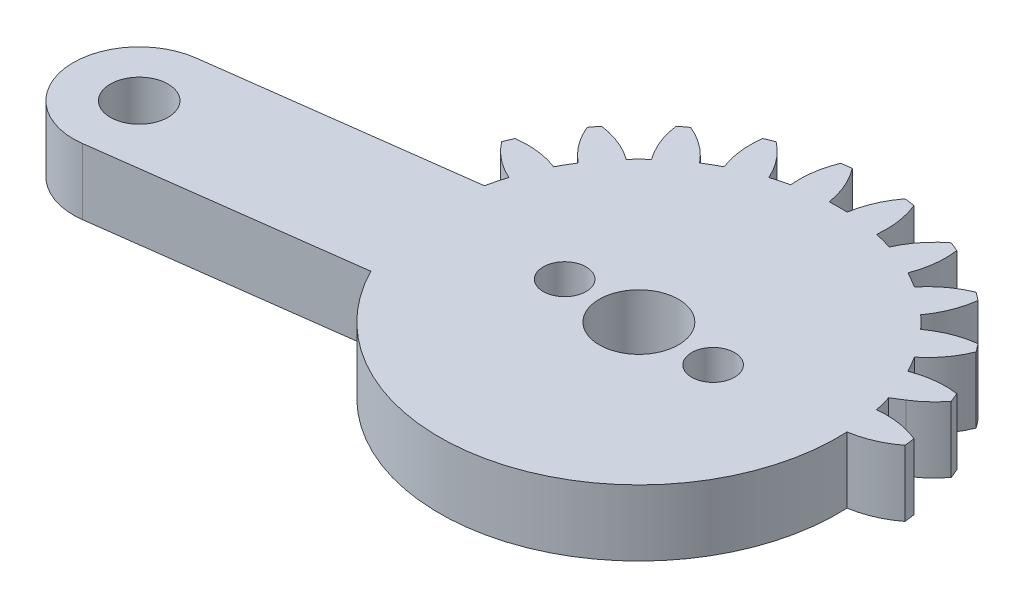
SolidWorks part; units mm, degrees
ref_plane "Front Plane" through (0, 0, 0) normal (0, 0, 1) x (1, 0, 0)
ref_plane "Top Plane" through (0, 0, 0) normal (0, 1, 0) x (1, 0, 0)
ref_plane "Right Plane" through (0, 0, 0) normal (1, 0, 0) x (0, 0, -1)
sketch "Sketch1" plane through (0, 0, 0) normal (0, 1, 0) x (1, 0, 0)
  line L0 (20.6437, 4) -> (2.0816, 4)
  line L1 (2.0816, -4) -> (20.6437, -4)
  arc A0 (2.0816, 4) -> (3.5217, 5.3071) centre (-0.7683, 8.5867) ccw
  arc A1 (3.5217, 5.3071) -> (3.2829, 5.8838) centre (-10.1063, 0) ccw
  arc A2 (3.2829, 5.8838) -> (0.6271, 5.5703) centre (2.5684, 0.5313) ccw
  arc A3 (0.6271, 5.5703) -> (0.0844, 6.5103) centre (-10.1063, 0) ccw
  arc A4 (0.0844, 6.5103) -> (1.6838, 8.6535) centre (-3.3089, 10.711) ccw
  arc A5 (1.6838, 8.6535) -> (1.3038, 9.1487) centre (-10.1063, 0) ccw
  arc A6 (1.3038, 9.1487) -> (-1.1803, 8.1585) centre (1.999, 3.7936) ccw
  arc A7 (-1.1803, 8.1585) -> (-1.9479, 8.926) centre (-10.1063, 0) ccw
  arc A8 (-1.9479, 8.926) -> (-0.9576, 11.4102) centre (-6.3127, 12.1053) ccw
  arc A9 (-0.9576, 11.4102) -> (-1.4528, 11.7901) centre (-10.1063, 0) ccw
  arc A10 (-1.4528, 11.7901) -> (-3.596, 10.1907) centre (0.6046, 6.7975) ccw
  arc A11 (-3.596, 10.1907) -> (-4.5361, 10.7334) centre (-10.1063, 0) ccw
  arc A12 (-4.5361, 10.7334) -> (-4.2225, 13.3892) centre (-9.5751, 12.6747) ccw
  arc A13 (-4.2225, 13.3892) -> (-4.7992, 13.6281) centre (-10.1063, 0) ccw
  arc A14 (-4.7992, 13.6281) -> (-6.4554, 11.5285) centre (-1.5196, 9.3381) ccw
  arc A15 (-6.4554, 11.5285) -> (-7.5039, 11.8094) centre (-10.1063, 0) ccw
  arc A16 (-7.5039, 11.8094) -> (-7.8884, 14.4558) centre (-12.8736, 12.3803) ccw
  arc A17 (-7.8884, 14.4558) -> (-8.5072, 14.5373) centre (-10.1063, 0) ccw
  arc A18 (-8.5072, 14.5373) -> (-9.5636, 12.0806) centre (-4.2291, 11.2423) ccw
  arc A19 (-9.5636, 12.0806) -> (-10.6491, 12.0806) centre (-10.1063, 0) ccw
  arc A20 (-10.6491, 12.0806) -> (-11.7054, 14.5373) centre (-15.9836, 11.2423) ccw
  arc A21 (-11.7054, 14.5373) -> (-12.3243, 14.4558) centre (-10.1063, 0) ccw
  arc A22 (-12.3243, 14.4558) -> (-12.7088, 11.8094) centre (-7.3391, 12.3803) ccw
  arc A23 (-12.7088, 11.8094) -> (-13.7573, 11.5285) centre (-10.1063, 0) ccw
  arc A24 (-13.7573, 11.5285) -> (-15.4135, 13.6281) centre (-18.6931, 9.3381) ccw
  arc A25 (-15.4135, 13.6281) -> (-15.9901, 13.3892) centre (-10.1063, 0) ccw
  arc A26 (-15.9901, 13.3892) -> (-15.6766, 10.7334) centre (-10.6376, 12.6747) ccw
  arc A27 (-15.6766, 10.7334) -> (-16.6166, 10.1907) centre (-10.1063, 0) ccw
  arc A28 (-16.6166, 10.1907) -> (-18.7599, 11.7901) centre (-20.8173, 6.7975) ccw
  arc A29 (-18.7599, 11.7901) -> (-19.255, 11.4102) centre (-10.1063, 0) ccw
  arc A30 (-19.255, 11.4102) -> (-18.2648, 8.926) centre (-13.9, 12.1053) ccw
  arc A31 (-18.2648, 8.926) -> (-19.0324, 8.1585) centre (-10.1063, 0) ccw
  arc A32 (-19.0324, 8.1585) -> (-21.5165, 9.1487) centre (-22.2117, 3.7936) ccw
  arc A33 (-21.5165, 9.1487) -> (-21.8965, 8.6535) centre (-10.1063, 0) ccw
  arc A34 (-21.8965, 8.6535) -> (-20.2971, 6.5103) centre (-16.9038, 10.711) ccw
  arc A35 (-20.2971, 6.5103) -> (-20.8398, 5.5703) centre (-10.1063, 0) ccw
  arc A36 (-20.8398, 5.5703) -> (-23.4956, 5.8838) centre (-22.7811, 0.5313) ccw
  arc A37 (-23.4956, 5.8838) -> (-23.7344, 5.3071) centre (-10.1063, 0) ccw
  arc A38 (-23.7344, 5.3071) -> (-21.6348, 3.6509) centre (-19.4444, 8.5867) ccw
  arc A39 (-21.6348, 3.6509) -> (-21.9157, 2.6025) centre (-10.1063, 0) ccw
  arc A40 (-21.9157, 2.6025) -> (-24.5622, 2.2179) centre (-22.4867, -2.7673) ccw
  arc A41 (-24.5622, 2.2179) -> (-24.6437, 1.5991) centre (-10.1063, 0) ccw
  arc A42 (-24.6437, 1.5991) -> (-22.1869, 0.5427) centre (-21.3486, 5.8773) ccw
  arc A43 (-22.1869, 0.5427) -> (-22.1869, -0.5427) centre (-10.1063, 0) ccw
  arc A44 (-22.1869, -0.5427) -> (-24.6437, -1.5991) centre (-21.3486, -5.8773) ccw
  arc A45 (-24.6437, -1.5991) -> (-24.5622, -2.2179) centre (-10.1063, 0) ccw
  arc A46 (-24.5622, -2.2179) -> (-21.9157, -2.6025) centre (-22.4867, 2.7673) ccw
  arc A47 (-21.9157, -2.6025) -> (-21.6348, -3.6509) centre (-10.1063, 0) ccw
  arc A48 (-21.6348, -3.6509) -> (-23.7344, -5.3071) centre (-19.4444, -8.5867) ccw
  arc A49 (-23.7344, -5.3071) -> (-23.4956, -5.8838) centre (-10.1063, 0) ccw
  arc A50 (-23.4956, -5.8838) -> (-20.8398, -5.5703) centre (-22.7811, -0.5313) ccw
  arc A51 (-20.8398, -5.5703) -> (-20.2971, -6.5103) centre (-10.1063, 0) ccw
  arc A52 (-20.2971, -6.5103) -> (-21.8965, -8.6535) centre (-16.9038, -10.711) ccw
  arc A53 (-21.8965, -8.6535) -> (-21.5165, -9.1487) centre (-10.1063, 0) ccw
  arc A54 (-21.5165, -9.1487) -> (-19.0324, -8.1585) centre (-22.2117, -3.7936) ccw
  arc A55 (-19.0324, -8.1585) -> (-18.2648, -8.926) centre (-10.1063, 0) ccw
  arc A56 (-18.2648, -8.926) -> (-19.255, -11.4102) centre (-13.9, -12.1053) ccw
  arc A57 (-19.255, -11.4102) -> (-18.7599, -11.7901) centre (-10.1063, 0) ccw
  arc A58 (-18.7599, -11.7901) -> (-16.6166, -10.1907) centre (-20.8173, -6.7975) ccw
  arc A59 (-16.6166, -10.1907) -> (-15.6766, -10.7334) centre (-10.1063, 0) ccw
  arc A60 (-15.6766, -10.7334) -> (-15.9901, -13.3892) centre (-10.6376, -12.6747) ccw
  arc A61 (-15.9901, -13.3892) -> (-15.4135, -13.6281) centre (-10.1063, 0) ccw
  arc A62 (-15.4135, -13.6281) -> (-13.7573, -11.5285) centre (-18.6931, -9.3381) ccw
  arc A63 (-13.7573, -11.5285) -> (-12.7088, -11.8094) centre (-10.1063, 0) ccw
  arc A64 (-12.7088, -11.8094) -> (-12.3243, -14.4558) centre (-7.3391, -12.3803) ccw
  arc A65 (-12.3243, -14.4558) -> (-11.7054, -14.5373) centre (-10.1063, 0) ccw
  arc A66 (-11.7054, -14.5373) -> (-10.6491, -12.0806) centre (-15.9836, -11.2423) ccw
  arc A67 (-10.6491, -12.0806) -> (-9.5636, -12.0806) centre (-10.1063, 0) ccw
  arc A68 (-9.5636, -12.0806) -> (-8.5072, -14.5373) centre (-4.2291, -11.2423) ccw
  arc A69 (-8.5072, -14.5373) -> (-7.8884, -14.4558) centre (-10.1063, 0) ccw
  arc A70 (-7.8884, -14.4558) -> (-7.5039, -11.8094) centre (-12.8736, -12.3803) ccw
  arc A71 (-7.5039, -11.8094) -> (-6.4554, -11.5285) centre (-10.1063, 0) ccw
  arc A72 (-6.4554, -11.5285) -> (-4.7992, -13.6281) centre (-1.5196, -9.3381) ccw
  arc A73 (-4.7992, -13.6281) -> (-4.2225, -13.3892) centre (-10.1063, 0) ccw
  arc A74 (-4.2225, -13.3892) -> (-4.5361, -10.7334) centre (-9.5751, -12.6747) ccw
  arc A75 (-4.5361, -10.7334) -> (-3.596, -10.1907) centre (-10.1063, 0) ccw
  arc A76 (-3.596, -10.1907) -> (-1.4528, -11.7901) centre (0.6046, -6.7975) ccw
  arc A77 (-1.4528, -11.7901) -> (-0.9576, -11.4102) centre (-10.1063, 0) ccw
  arc A78 (-0.9576, -11.4102) -> (-1.9479, -8.926) centre (-6.3127, -12.1053) ccw
  arc A79 (-1.9479, -8.926) -> (-1.1803, -8.1585) centre (-10.1063, 0) ccw
  arc A80 (-1.1803, -8.1585) -> (1.3038, -9.1487) centre (1.999, -3.7936) ccw
  arc A81 (1.3038, -9.1487) -> (1.6838, -8.6535) centre (-10.1063, 0) ccw
  arc A82 (1.6838, -8.6535) -> (0.0844, -6.5103) centre (-3.3089, -10.711) ccw
  arc A83 (0.0844, -6.5103) -> (0.6271, -5.5703) centre (-10.1063, 0) ccw
  arc A84 (0.6271, -5.5703) -> (3.2829, -5.8838) centre (2.5684, -0.5313) ccw
  arc A85 (3.2829, -5.8838) -> (3.5217, -5.3071) centre (-10.1063, 0) ccw
  arc A86 (3.5217, -5.3071) -> (2.0816, -4) centre (-0.7683, -8.5867) ccw
  arc A87 (20.6437, -4) -> (20.6437, 4) centre (20.6437, 0) ccw
  circle A88 centre (-10.1063, 0) radius 1.5
  circle A89 centre (20.6437, 0) radius 1.5
  dimension "D1" = 3
  dimension "D2" = 3
extrude "Boss-Extrude1" add sketch "Sketch1" along normal blind 4
sketch "Sketch3" plane through (0, 4, 0) normal (0, 1, 0) x (1, 0, 0)
  line L0 (-10.1063, 0) -> (-40.8563, 0) construction
  line L1 (-10.1063, 0) -> (-36.8754, -3.5242)
  line L2 (-10.6284, 3.9658) -> (-37.3975, 0.4416)
  line L3 (-9.5842, -3.9658) -> (-36.3532, -7.49)
  line L4 (-10.1063, 0) -> (-4.5096, 13.5117) construction
  line L5 (-10.1063, 0) -> (-8.1974, 14.4999) construction
  circle A0 centre (-10.1063, 0) radius 1.5
  circle A1 centre (20.6437, 0) radius 1.5 construction
  circle A2 centre (20.6437, 0) radius 1.5
  circle A3 centre (-36.8754, -3.5242) radius 1.75
  circle A4 centre (-36.8754, -3.5242) radius 4
  circle A5 centre (-10.1063, 0) radius 4
  arc A6 (-4.2225, 13.3892) -> (-4.7992, 13.6281) centre (-10.1063, 0) ccw construction
  arc A7 (-7.8884, 14.4558) -> (-8.5072, 14.5373) centre (-10.1063, 0) ccw construction
  dimension "D2" = 3
  dimension "D5" = 3.5
  dimension "D6" = 8
  dimension "D7" = 8
  dimension "D1" = 27
  dimension "D4" = 7.5
extrude "Boss-Extrude2" add sketch "Sketch3" against normal blind 4
sketch "Sketch4" plane through (0, 4, 0) normal (0, 1, 0) x (1, 0, 0)
  line L0 (20.6437, 4) -> (2.0816, 4) construction
  line L1 (2.0816, -4) -> (20.6437, -4) construction
  line L2 (20.6437, 4) -> (2.0816, 4)
  line L3 (2.0816, -4) -> (20.6437, -4)
  line L4 (2.0816, 4) -> (1.4381, 3.6001)
  line L5 (-21.6245, -5.5509) -> (-20.8986, -5.4553)
  line L6 (-10.1063, 0) -> (0.0844, 6.5103) construction
  line L7 (-10.1063, 0) -> (1.9742, 0.5427) construction
  line L8 (-24.5755, 2.1296) -> (-37.3975, 0.4416)
  line L9 (-36.3532, -7.49) -> (-23.5312, -5.8019)
  line L10 (2.0816, -4) -> (20.6437, -4)
  line L11 (20.6437, 4) -> (2.0816, 4)
  line L12 (-21.9429, 2.4762) -> (-37.3975, 0.4416)
  line L13 (-36.3532, -7.49) -> (-21.6245, -5.5509)
  line L14 (2.0816, -4) -> (20.6437, -4)
  line L15 (20.6437, 4) -> (2.0816, 4)
  circle A0 centre (-10.1063, 0) radius 12.0927
  arc A1 (3.2829, 5.8838) -> (0.6271, 5.5703) centre (2.5684, 0.5313) ccw construction
  arc A2 (3.5217, 5.3071) -> (3.2829, 5.8838) centre (-10.1063, 0) ccw construction
  arc A3 (2.0816, 4) -> (3.5217, 5.3071) centre (-0.7683, 8.5867) ccw construction
  arc A4 (20.6437, -4) -> (20.6437, 4) centre (20.6437, 0) ccw construction
  arc A5 (3.5217, -5.3071) -> (2.0816, -4) centre (-0.7683, -8.5867) ccw construction
  arc A6 (3.2829, -5.8838) -> (3.5217, -5.3071) centre (-10.1063, 0) ccw construction
  arc A7 (0.6271, -5.5703) -> (3.2829, -5.8838) centre (2.5684, -0.5313) ccw construction
  arc A8 (3.2829, 5.8838) -> (0.6271, 5.5703) centre (2.5684, 0.5313) ccw
  arc A9 (3.5217, 5.3071) -> (3.2829, 5.8838) centre (-10.1063, 0) ccw
  arc A10 (2.0816, 4) -> (3.5217, 5.3071) centre (-0.7683, 8.5867) ccw
  arc A11 (20.6437, -4) -> (20.6437, 4) centre (20.6437, 0) ccw
  arc A12 (3.5217, -5.3071) -> (2.0816, -4) centre (-0.7683, -8.5867) ccw
  arc A13 (3.2829, -5.8838) -> (3.5217, -5.3071) centre (-10.1063, 0) ccw
  arc A14 (0.6271, -5.5703) -> (3.2829, -5.8838) centre (2.5684, -0.5313) ccw
  arc A15 (1.9742, 0.5427) -> (4.431, 1.5991) centre (1.1359, 5.8773) ccw
  arc A16 (4.3495, 2.2179) -> (1.7031, 2.6025) centre (2.274, -2.7673) ccw
  arc A17 (4.431, 1.5991) -> (4.3495, 2.2179) centre (-10.1063, 0) ccw
  arc A95 (-21.6348, 3.6509) -> (-21.9157, 2.6025) centre (-10.1063, 0) ccw
  arc A96 (-37.3975, 0.4416) -> (-36.3532, -7.49) centre (-36.8754, -3.5242) ccw
  arc A97 (-20.2971, -6.5103) -> (-21.8965, -8.6535) centre (-16.9038, -10.711) ccw
  arc A98 (-21.8965, -8.6535) -> (-21.5165, -9.1487) centre (-10.1063, 0) ccw
  arc A99 (-21.5165, -9.1487) -> (-19.0324, -8.1585) centre (-22.2117, -3.7936) ccw
  arc A100 (-19.0324, -8.1585) -> (-18.2648, -8.926) centre (-10.1063, 0) ccw
  arc A101 (-18.2648, -8.926) -> (-19.255, -11.4102) centre (-13.9, -12.1053) ccw
  arc A102 (-19.255, -11.4102) -> (-18.7599, -11.7901) centre (-10.1063, 0) ccw
  arc A103 (-18.7599, -11.7901) -> (-16.6166, -10.1907) centre (-20.8173, -6.7975) ccw
  arc A104 (-16.6166, -10.1907) -> (-15.6766, -10.7334) centre (-10.1063, 0) ccw
  arc A105 (-15.6766, -10.7334) -> (-15.9901, -13.3892) centre (-10.6376, -12.6747) ccw
  arc A106 (-15.9901, -13.3892) -> (-15.4135, -13.6281) centre (-10.1063, 0) ccw
  arc A107 (-15.4135, -13.6281) -> (-13.7573, -11.5285) centre (-18.6931, -9.3381) ccw
  arc A108 (-13.7573, -11.5285) -> (-12.7088, -11.8094) centre (-10.1063, 0) ccw
  arc A109 (-12.7088, -11.8094) -> (-12.3243, -14.4558) centre (-7.3391, -12.3803) ccw
  arc A110 (-12.3243, -14.4558) -> (-11.7054, -14.5373) centre (-10.1063, 0) ccw
  arc A111 (-11.7054, -14.5373) -> (-10.6491, -12.0806) centre (-15.9836, -11.2423) ccw
  arc A112 (-10.6491, -12.0806) -> (-9.5636, -12.0806) centre (-10.1063, 0) ccw
  arc A113 (-9.5636, -12.0806) -> (-8.5072, -14.5373) centre (-4.2291, -11.2423) ccw
  arc A114 (-8.5072, -14.5373) -> (-7.8884, -14.4558) centre (-10.1063, 0) ccw
  arc A115 (-7.8884, -14.4558) -> (-7.5039, -11.8094) centre (-12.8736, -12.3803) ccw
  arc A116 (-7.5039, -11.8094) -> (-6.4554, -11.5285) centre (-10.1063, 0) ccw
  arc A117 (-6.4554, -11.5285) -> (-4.7992, -13.6281) centre (-1.5196, -9.3381) ccw
  arc A118 (-4.7992, -13.6281) -> (-4.2225, -13.3892) centre (-10.1063, 0) ccw
  arc A119 (-4.2225, -13.3892) -> (-4.5361, -10.7334) centre (-9.5751, -12.6747) ccw
  arc A120 (-4.5361, -10.7334) -> (-3.596, -10.1907) centre (-10.1063, 0) ccw
  arc A121 (-3.596, -10.1907) -> (-1.4528, -11.7901) centre (0.6046, -6.7975) ccw
  arc A122 (-1.4528, -11.7901) -> (-0.9576, -11.4102) centre (-10.1063, 0) ccw
  arc A123 (-0.9576, -11.4102) -> (-1.9479, -8.926) centre (-6.3127, -12.1053) ccw
  arc A124 (-1.9479, -8.926) -> (-1.1803, -8.1585) centre (-10.1063, 0) ccw
  arc A125 (-1.1803, -8.1585) -> (1.3038, -9.1487) centre (1.999, -3.7936) ccw
  arc A126 (1.3038, -9.1487) -> (1.6838, -8.6535) centre (-10.1063, 0) ccw
  arc A127 (1.6838, -8.6535) -> (0.0844, -6.5103) centre (-3.3089, -10.711) ccw
  arc A128 (0.0844, -6.5103) -> (0.6271, -5.5703) centre (-10.1063, 0) ccw
  arc A129 (0.6271, -5.5703) -> (3.2829, -5.8838) centre (2.5684, -0.5313) ccw
  arc A130 (3.2829, -5.8838) -> (3.5217, -5.3071) centre (-10.1063, 0) ccw
  arc A131 (3.5217, -5.3071) -> (2.0816, -4) centre (-0.7683, -8.5867) ccw
  arc A132 (20.6437, -4) -> (20.6437, 4) centre (20.6437, 0) ccw
  arc A133 (2.0816, 4) -> (3.5217, 5.3071) centre (-0.7683, 8.5867) ccw
  arc A134 (3.5217, 5.3071) -> (3.2829, 5.8838) centre (-10.1063, 0) ccw
  arc A135 (3.2829, 5.8838) -> (0.6271, 5.5703) centre (2.5684, 0.5313) ccw
  arc A136 (0.6271, 5.5703) -> (0.0844, 6.5103) centre (-10.1063, 0) ccw
  arc A137 (0.0844, 6.5103) -> (1.6838, 8.6535) centre (-3.3089, 10.711) ccw
  arc A138 (1.6838, 8.6535) -> (1.3038, 9.1487) centre (-10.1063, 0) ccw
  arc A139 (1.3038, 9.1487) -> (-1.1803, 8.1585) centre (1.999, 3.7936) ccw
  arc A140 (-1.1803, 8.1585) -> (-1.9479, 8.926) centre (-10.1063, 0) ccw
  arc A141 (-1.9479, 8.926) -> (-0.9576, 11.4102) centre (-6.3127, 12.1053) ccw
  arc A142 (-0.9576, 11.4102) -> (-1.4528, 11.7901) centre (-10.1063, 0) ccw
  arc A143 (-1.4528, 11.7901) -> (-3.596, 10.1907) centre (0.6046, 6.7975) ccw
  arc A144 (-3.596, 10.1907) -> (-4.5361, 10.7334) centre (-10.1063, 0) ccw
  arc A145 (-4.5361, 10.7334) -> (-4.2225, 13.3892) centre (-9.5751, 12.6747) ccw
  arc A146 (-4.2225, 13.3892) -> (-4.7992, 13.6281) centre (-10.1063, 0) ccw
  arc A147 (-4.7992, 13.6281) -> (-6.4554, 11.5285) centre (-1.5196, 9.3381) ccw
  arc A148 (-6.4554, 11.5285) -> (-7.5039, 11.8094) centre (-10.1063, 0) ccw
  arc A149 (-7.5039, 11.8094) -> (-7.8884, 14.4558) centre (-12.8736, 12.3803) ccw
  arc A150 (-7.8884, 14.4558) -> (-8.5072, 14.5373) centre (-10.1063, 0) ccw
  arc A151 (-8.5072, 14.5373) -> (-9.5636, 12.0806) centre (-4.2291, 11.2423) ccw
  arc A152 (-9.5636, 12.0806) -> (-10.6491, 12.0806) centre (-10.1063, 0) ccw
  arc A153 (-10.6491, 12.0806) -> (-11.7054, 14.5373) centre (-15.9836, 11.2423) ccw
  arc A154 (-11.7054, 14.5373) -> (-12.3243, 14.4558) centre (-10.1063, 0) ccw
  arc A155 (-12.3243, 14.4558) -> (-12.7088, 11.8094) centre (-7.3391, 12.3803) ccw
  arc A156 (-12.7088, 11.8094) -> (-13.7573, 11.5285) centre (-10.1063, 0) ccw
  arc A157 (-13.7573, 11.5285) -> (-15.4135, 13.6281) centre (-18.6931, 9.3381) ccw
  arc A158 (-15.4135, 13.6281) -> (-15.9901, 13.3892) centre (-10.1063, 0) ccw
  arc A159 (-15.9901, 13.3892) -> (-15.6766, 10.7334) centre (-10.6376, 12.6747) ccw
  arc A160 (-15.6766, 10.7334) -> (-16.6166, 10.1907) centre (-10.1063, 0) ccw
  arc A161 (-16.6166, 10.1907) -> (-18.7599, 11.7901) centre (-20.8173, 6.7975) ccw
  arc A162 (-18.7599, 11.7901) -> (-19.255, 11.4102) centre (-10.1063, 0) ccw
  arc A163 (-19.255, 11.4102) -> (-18.2648, 8.926) centre (-13.9, 12.1053) ccw
  arc A164 (-18.2648, 8.926) -> (-19.0324, 8.1585) centre (-10.1063, 0) ccw
  arc A165 (-19.0324, 8.1585) -> (-21.5165, 9.1487) centre (-22.2117, 3.7936) ccw
  arc A166 (-21.5165, 9.1487) -> (-21.8965, 8.6535) centre (-10.1063, 0) ccw
  arc A167 (-21.8965, 8.6535) -> (-20.2971, 6.5103) centre (-16.9038, 10.711) ccw
  arc A168 (-20.2971, 6.5103) -> (-20.8398, 5.5703) centre (-10.1063, 0) ccw
  arc A169 (-20.8398, 5.5703) -> (-23.4956, 5.8838) centre (-22.7811, 0.5313) ccw
  arc A170 (-23.4956, 5.8838) -> (-23.7344, 5.3071) centre (-10.1063, 0) ccw
  arc A171 (-23.7344, 5.3071) -> (-21.6348, 3.6509) centre (-19.4444, 8.5867) ccw
  arc A172 (-21.6348, 3.6509) -> (-21.9157, 2.6025) centre (-10.1063, 0) ccw
  arc A175 (-23.4956, -5.8838) -> (-20.8398, -5.5703) centre (-22.7811, -0.5313) ccw
  arc A176 (-37.3975, 0.4416) -> (-36.3532, -7.49) centre (-36.8754, -3.5242) ccw
  arc A177 (-20.2971, -6.5103) -> (-21.8965, -8.6535) centre (-16.9038, -10.711) ccw
  arc A178 (-21.8965, -8.6535) -> (-21.5165, -9.1487) centre (-10.1063, 0) ccw
  arc A179 (-21.5165, -9.1487) -> (-19.0324, -8.1585) centre (-22.2117, -3.7936) ccw
  arc A180 (-19.0324, -8.1585) -> (-18.2648, -8.926) centre (-10.1063, 0) ccw
  arc A181 (-18.2648, -8.926) -> (-19.255, -11.4102) centre (-13.9, -12.1053) ccw
  arc A182 (-19.255, -11.4102) -> (-18.7599, -11.7901) centre (-10.1063, 0) ccw
  arc A183 (-18.7599, -11.7901) -> (-16.6166, -10.1907) centre (-20.8173, -6.7975) ccw
  arc A184 (-16.6166, -10.1907) -> (-15.6766, -10.7334) centre (-10.1063, 0) ccw
  arc A185 (-15.6766, -10.7334) -> (-15.9901, -13.3892) centre (-10.6376, -12.6747) ccw
  arc A186 (-15.9901, -13.3892) -> (-15.4135, -13.6281) centre (-10.1063, 0) ccw
  arc A187 (-15.4135, -13.6281) -> (-13.7573, -11.5285) centre (-18.6931, -9.3381) ccw
  arc A188 (-13.7573, -11.5285) -> (-12.7088, -11.8094) centre (-10.1063, 0) ccw
  arc A189 (-12.7088, -11.8094) -> (-12.3243, -14.4558) centre (-7.3391, -12.3803) ccw
  arc A190 (-12.3243, -14.4558) -> (-11.7054, -14.5373) centre (-10.1063, 0) ccw
  arc A191 (-11.7054, -14.5373) -> (-10.6491, -12.0806) centre (-15.9836, -11.2423) ccw
  arc A192 (-10.6491, -12.0806) -> (-9.5636, -12.0806) centre (-10.1063, 0) ccw
  arc A193 (-9.5636, -12.0806) -> (-8.5072, -14.5373) centre (-4.2291, -11.2423) ccw
  arc A194 (-8.5072, -14.5373) -> (-7.8884, -14.4558) centre (-10.1063, 0) ccw
  arc A195 (-7.8884, -14.4558) -> (-7.5039, -11.8094) centre (-12.8736, -12.3803) ccw
  arc A196 (-7.5039, -11.8094) -> (-6.4554, -11.5285) centre (-10.1063, 0) ccw
  arc A197 (-6.4554, -11.5285) -> (-4.7992, -13.6281) centre (-1.5196, -9.3381) ccw
  arc A198 (-4.7992, -13.6281) -> (-4.2225, -13.3892) centre (-10.1063, 0) ccw
  arc A199 (-4.2225, -13.3892) -> (-4.5361, -10.7334) centre (-9.5751, -12.6747) ccw
  arc A200 (-4.5361, -10.7334) -> (-3.596, -10.1907) centre (-10.1063, 0) ccw
  arc A201 (-3.596, -10.1907) -> (-1.4528, -11.7901) centre (0.6046, -6.7975) ccw
  arc A202 (-1.4528, -11.7901) -> (-0.9576, -11.4102) centre (-10.1063, 0) ccw
  arc A203 (-0.9576, -11.4102) -> (-1.9479, -8.926) centre (-6.3127, -12.1053) ccw
  arc A204 (-1.9479, -8.926) -> (-1.1803, -8.1585) centre (-10.1063, 0) ccw
  arc A205 (-1.1803, -8.1585) -> (1.3038, -9.1487) centre (1.999, -3.7936) ccw
  arc A206 (1.3038, -9.1487) -> (1.6838, -8.6535) centre (-10.1063, 0) ccw
  arc A207 (1.6838, -8.6535) -> (0.0844, -6.5103) centre (-3.3089, -10.711) ccw
  arc A208 (0.0844, -6.5103) -> (0.6271, -5.5703) centre (-10.1063, 0) ccw
  arc A209 (0.6271, -5.5703) -> (3.2829, -5.8838) centre (2.5684, -0.5313) ccw
  arc A210 (3.2829, -5.8838) -> (3.5217, -5.3071) centre (-10.1063, 0) ccw
  arc A211 (3.5217, -5.3071) -> (2.0816, -4) centre (-0.7683, -8.5867) ccw
  arc A212 (20.6437, -4) -> (20.6437, 4) centre (20.6437, 0) ccw
  arc A213 (2.0816, 4) -> (3.5217, 5.3071) centre (-0.7683, 8.5867) ccw
  arc A214 (3.5217, 5.3071) -> (3.2829, 5.8838) centre (-10.1063, 0) ccw
  arc A215 (3.2829, 5.8838) -> (0.6271, 5.5703) centre (2.5684, 0.5313) ccw
  arc A216 (0.6271, 5.5703) -> (0.0844, 6.5103) centre (-10.1063, 0) ccw
  arc A217 (0.0844, 6.5103) -> (1.6838, 8.6535) centre (-3.3089, 10.711) ccw
  arc A218 (1.6838, 8.6535) -> (1.3038, 9.1487) centre (-10.1063, 0) ccw
  arc A219 (1.3038, 9.1487) -> (-1.1803, 8.1585) centre (1.999, 3.7936) ccw
  arc A220 (-1.1803, 8.1585) -> (-1.9479, 8.926) centre (-10.1063, 0) ccw
  arc A221 (-1.9479, 8.926) -> (-0.9576, 11.4102) centre (-6.3127, 12.1053) ccw
  arc A222 (-0.9576, 11.4102) -> (-1.4528, 11.7901) centre (-10.1063, 0) ccw
  arc A223 (-1.4528, 11.7901) -> (-3.596, 10.1907) centre (0.6046, 6.7975) ccw
  arc A224 (-3.596, 10.1907) -> (-4.5361, 10.7334) centre (-10.1063, 0) ccw
  arc A225 (-4.5361, 10.7334) -> (-4.2225, 13.3892) centre (-9.5751, 12.6747) ccw
  arc A226 (-4.2225, 13.3892) -> (-4.7992, 13.6281) centre (-10.1063, 0) ccw
  arc A227 (-4.7992, 13.6281) -> (-6.4554, 11.5285) centre (-1.5196, 9.3381) ccw
  arc A228 (-6.4554, 11.5285) -> (-7.5039, 11.8094) centre (-10.1063, 0) ccw
  arc A229 (-7.5039, 11.8094) -> (-7.8884, 14.4558) centre (-12.8736, 12.3803) ccw
  arc A230 (-7.8884, 14.4558) -> (-8.5072, 14.5373) centre (-10.1063, 0) ccw
  arc A231 (-8.5072, 14.5373) -> (-9.5636, 12.0806) centre (-4.2291, 11.2423) ccw
  arc A232 (-9.5636, 12.0806) -> (-10.6491, 12.0806) centre (-10.1063, 0) ccw
  arc A233 (-10.6491, 12.0806) -> (-11.7054, 14.5373) centre (-15.9836, 11.2423) ccw
  arc A234 (-11.7054, 14.5373) -> (-12.3243, 14.4558) centre (-10.1063, 0) ccw
  arc A235 (-12.3243, 14.4558) -> (-12.7088, 11.8094) centre (-7.3391, 12.3803) ccw
  arc A236 (-12.7088, 11.8094) -> (-13.7573, 11.5285) centre (-10.1063, 0) ccw
  arc A237 (-13.7573, 11.5285) -> (-15.4135, 13.6281) centre (-18.6931, 9.3381) ccw
  arc A238 (-15.4135, 13.6281) -> (-15.9901, 13.3892) centre (-10.1063, 0) ccw
  arc A239 (-15.9901, 13.3892) -> (-15.6766, 10.7334) centre (-10.6376, 12.6747) ccw
  arc A240 (-15.6766, 10.7334) -> (-16.6166, 10.1907) centre (-10.1063, 0) ccw
  arc A241 (-16.6166, 10.1907) -> (-18.7599, 11.7901) centre (-20.8173, 6.7975) ccw
  arc A242 (-18.7599, 11.7901) -> (-19.255, 11.4102) centre (-10.1063, 0) ccw
  arc A243 (-19.255, 11.4102) -> (-18.2648, 8.926) centre (-13.9, 12.1053) ccw
  arc A244 (-18.2648, 8.926) -> (-19.0324, 8.1585) centre (-10.1063, 0) ccw
  arc A245 (-19.0324, 8.1585) -> (-21.5165, 9.1487) centre (-22.2117, 3.7936) ccw
  arc A246 (-21.5165, 9.1487) -> (-21.8965, 8.6535) centre (-10.1063, 0) ccw
  arc A247 (-21.8965, 8.6535) -> (-20.2971, 6.5103) centre (-16.9038, 10.711) ccw
  arc A248 (-20.2971, 6.5103) -> (-20.8398, 5.5703) centre (-10.1063, 0) ccw
  arc A249 (-20.8398, 5.5703) -> (-23.4956, 5.8838) centre (-22.7811, 0.5313) ccw
  arc A250 (-23.4956, 5.8838) -> (-23.7344, 5.3071) centre (-10.1063, 0) ccw
  arc A251 (-23.7344, 5.3071) -> (-21.6348, 3.6509) centre (-19.4444, 8.5867) ccw
  arc A252 (-23.4956, -5.8838) -> (-20.8398, -5.5703) centre (-22.7811, -0.5313) ccw
  arc A253 (-20.8398, -5.5703) -> (-20.2971, -6.5103) centre (-10.1063, 0) ccw
  arc A254 (-20.8398, -5.5703) -> (-20.2971, -6.5103) centre (-10.1063, 0) ccw
  arc A255 (-23.5312, -5.8019) -> (-23.4956, -5.8838) centre (-10.1063, 0) ccw
  arc A256 (-23.5312, -5.8019) -> (-23.4956, -5.8838) centre (-10.1063, 0) ccw
  arc A257 (-21.9157, 2.6025) -> (-24.5622, 2.2179) centre (-22.4867, -2.7673) ccw
  arc A258 (-21.9157, 2.6025) -> (-24.5622, 2.2179) centre (-22.4867, -2.7673) ccw
  arc A259 (-24.5622, 2.2179) -> (-24.5755, 2.1296) centre (-10.1063, 0) ccw
  arc A260 (-24.5622, 2.2179) -> (-24.5755, 2.1296) centre (-10.1063, 0) ccw
  point P40 (-10.1063, 0)
  dimension "D2" = 24.1855
  dimension "D4" = 30
  dimension "D1" = 0
  dimension "D3" = 2
extrude "Cut-Extrude1" cut sketch "Sketch4" against normal blind 4 contours A178 A179 A0 L5 A177 | A182 A183 A0 A181 | A186 A187 A0 A185 | A190 A191 A0 A189 | A194 A195 A0 A193 | A198 A199 A0 A197 | A202 A203 A0 A201 | A206 A207 A0 A205 | A258 A260 L12 A0 | L13 A256 A252 A0 L5 | A0 A14 A13 A12 L3 A11 L2 L4
sketch "Sketch5" plane through (0, 4, 0) normal (0, 1, 0) x (1, 0, 0)
  circle A0 centre (-10.1063, 0) radius 2.4
  circle A1 centre (-5.6063, 0) radius 1.3
  circle A2 centre (-14.6063, 0) radius 1.3
  circle A3 centre (-10.1063, 0) radius 1.5 construction
  dimension "D1" = 4.8
  dimension "D2" = 2.6
  dimension "D3" = 2.6
  dimension "D4" = 4.5
  dimension "D5" = 9
extrude "Cut-Extrude2" cut sketch "Sketch5" against normal up to next contours A2 | A1 | A0
